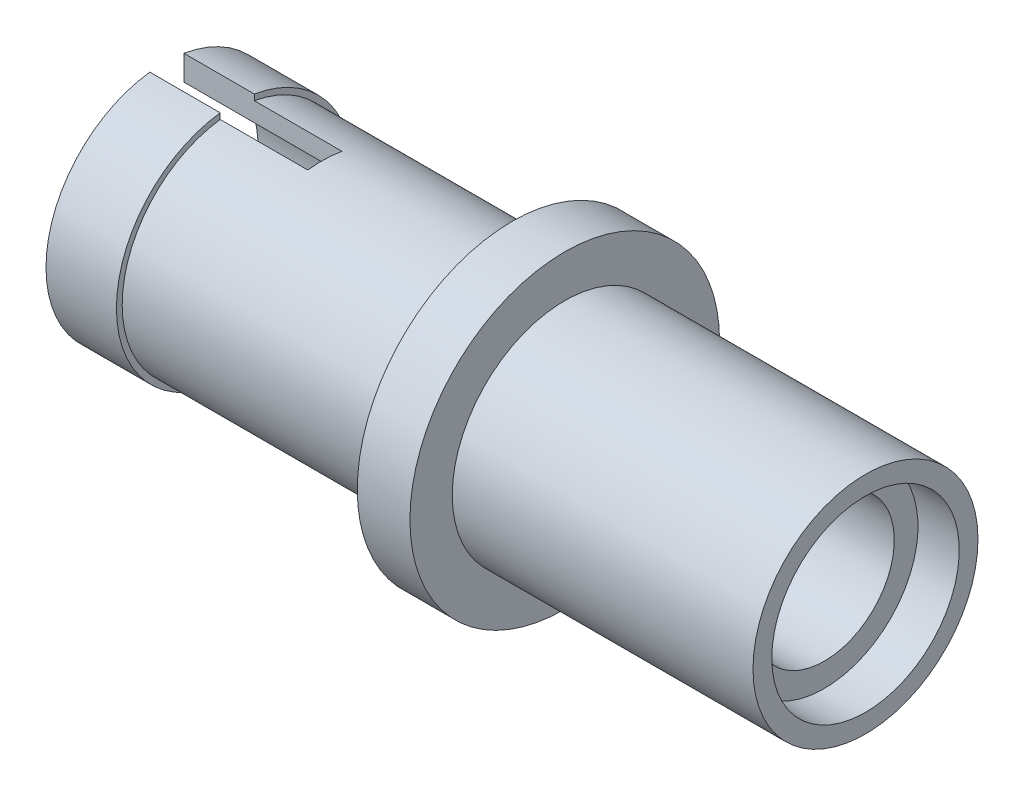
SolidWorks part; units mm, degrees
ref_plane "Front Plane" through (0, 0, 0) normal (0, 0, 1) x (1, 0, 0)
ref_plane "Top Plane" through (0, 0, 0) normal (0, 1, 0) x (1, 0, 0)
ref_plane "Right Plane" through (0, 0, 0) normal (1, 0, 0) x (0, 0, -1)
sketch "Sketch1" plane through (0, 0, 0) normal (0, 0, 1) x (1, 0, 0)
  line L0 (-64.0464, 7.115) -> (-57.6494, 7.115)
  line L1 (-57.6494, 7.115) -> (-57.6494, 6.353)
  line L2 (-57.6494, 6.353) -> (-52.8637, 6.353)
  line L3 (-52.8637, 6.353) -> (-52.8637, 4.1017)
  line L4 (-52.8637, 4.1017) -> (-51.1708, 4.1017)
  line L5 (-51.1708, 4.1017) -> (-51.1708, 6.353)
  line L6 (-51.1708, 6.353) -> (-42.8284, 6.353)
  line L7 (-42.8284, 6.353) -> (-42.8284, 7.115)
  line L8 (-42.8284, 7.115) -> (-41.5029, 7.115)
  line L9 (-41.5029, 7.115) -> (-41.5029, 7.7182)
  line L10 (-41.5029, 7.7182) -> (-51.1708, 7.7182)
  line L11 (-51.1708, 7.7182) -> (-51.1708, 9.0787)
  line L12 (-51.1708, 9.0787) -> (-52.8637, 9.0787)
  line L13 (-52.8637, 9.0787) -> (-52.8637, 7.7182)
  line L14 (-52.8637, 7.7182) -> (-54.8629, 7.7182)
  line L15 (-54.8629, 7.7182) -> (-55.9614, 7.7182)
  line L16 (-55.9614, 7.7182) -> (-58.857, 7.7182)
  line L17 (-64.0464, 7.115) -> (-64.0464, 7.9028)
  line L18 (-64.0464, 7.9028) -> (-61.7819, 7.9028)
  line L19 (-61.7819, 7.9028) -> (-61.7819, 7.7182)
  line L20 (-61.7819, 7.7182) -> (-59.4837, 7.7182)
  line L21 (-59.4837, 7.7182) -> (-58.857, 7.7182)
  point P2 (0, 0)
  point P23 (0, 0)
  point P24 (0, 0)
  point P25 (0, 0)
  point P26 (0, 0)
  point P27 (0, 0)
  point P28 (-55.9614, 7.7182)
  point P29 (0, 0)
  point P30 (-62.2958, 7.516)
  point P31 (-60.1178, 7.5816)
  point P32 (-61.9633, 7.5491)
  point P33 (0, 0)
  point P34 (-62.6782, 7.7654)
  point P35 (0, 0)
  point P36 (0, 0)
  point P37 (-61.7819, 7.7477)
  point P38 (-59.2539, 7.7451)
  point P39 (0, 0)
  point P40 (-59.4837, 7.7182)
  point P41 (-64.0464, 7.9028)
  dimension "D1" = 0.762
revolve "Revolve3" add sketch "Sketch1" angle 360 about L4
sketch "Sketch4" plane through (-64.0464, 0, 0) normal (-1, 0, 0) x (0, 0, 1)
  line L0 (-0.6316, 7.85) -> (-0.6316, 8.2195)
  line L2 (-0.6316, 7.85) -> (-0.6316, 0.3291)
  line L4 (0.4645, 7.85) -> (0.4645, 0.3291)
  line L5 (-0.6316, 8.2195) -> (0.4645, 8.2195)
  line L6 (0.4645, 8.2195) -> (0.4645, 7.85)
  line L7 (-0.6316, 0.3291) -> (-0.3701, 0)
  line L8 (-0.3701, 0) -> (0.4645, 0.3291)
  circle A0 centre (0, 4.1017) radius 3.8011 construction
extrude "Cut-Extrude1" cut sketch "Sketch4" against normal blind 5.08
